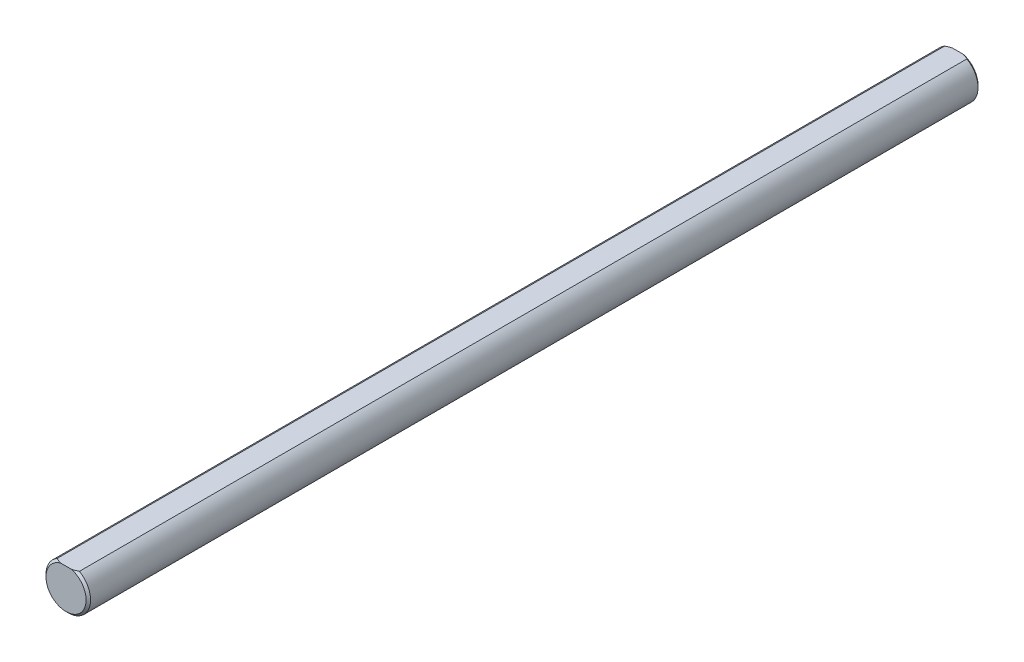
SolidWorks part; units mm, degrees
ref_plane "Front Plane" through (0, 0, 0) normal (0, 0, 1) x (1, 0, 0)
ref_plane "Top Plane" through (0, 0, 0) normal (0, 1, 0) x (1, 0, 0)
ref_plane "Right Plane" through (0, 0, 0) normal (1, 0, 0) x (0, 0, -1)
sketch "Sketch1" plane through (0, 0, 0) normal (0, 0, 1) x (1, 0, 0)
  line L0 (2.5, 4.3301) -> (-2.5, 4.3301) construction
  line L1 (0, 4.3301) -> (0, 0) construction
  line L2 (0, 0) -> (0, -5) construction
  circle A1 centre (0, 0) radius 5 construction
  dimension "Diameter" = 10
  dimension "Flat Width" = 5
  dimension "D1" = 9.3301
sketch "Sketch2" plane through (0, 0, 0) normal (1, 0, 0) x (0, 0, -1)
  line L0 (-100, 5) -> (100, 5) construction
  line L1 (0, 5) -> (0, -5) construction
  line L2 (0, 5) -> (0, -5) construction
  line L3 (-100, 5) -> (-100, 0) construction
  line L4 (-100, 0) -> (0, 0) construction
  line L6 (-100, 4.5) -> (-99.5, 5) construction
  point P2 (0, 5)
  point P3 (80, 5)
  point P4 (-80, 5)
  dimension "Length/ D-Profile Length" = 200
  dimension "D2" = 20
  dimension "D1" = 20
  dimension "Chamfer Typ." = 45
  dimension "D4" = 0.5
sketch "Sketch3" plane through (0, 0, 0) normal (0, 0, 1) x (1, 0, 0)
  circle A1 centre (0, 0) radius 5 construction
  circle A3 centre (0, 0) radius 5
extrude "Boss-Extrude2" add sketch "Sketch3" along normal up to vertex (100 mm away) and the other way up to vertex (100 mm away) up to point (0, 5, 100) other way up to point (0, 5, -100)
sketch "Sketch10" plane through (0, 0, 0) normal (0, 0, 1) x (1, 0, 0)
  line L0 (-2.5, 4.3301) -> (2.5, 4.3301)
  line L1 (0, 0) -> (0, 5) construction
  circle A0 centre (0, 0) radius 5 construction
  circle A1 centre (0, 0) radius 5 construction
  arc A2 (-2.5, 4.3301) -> (2.5, 4.3301) centre (0, 0) cw
extrude "Cut-Extrude5" cut sketch "Sketch10" against normal through all both and the other way through all
chamfer "Chamfer1" distance 0.5 angle 45 4 edges at (0, -5, 100) (0, -5, -100) (0, 4.3301, -100) (0, 4.3301, 100)
equation "\"D1@Chamfer1\"= \"Diameter@Sketch1\" / 20"
equation "\"D1@Sketch2\"=\"Diameter@Sketch1\"*2"
equation "\"D2@Sketch2\"=\"D1@Sketch2\""
equation "\"D4@Sketch2\"=\"Diameter@Sketch1\" / 20"
